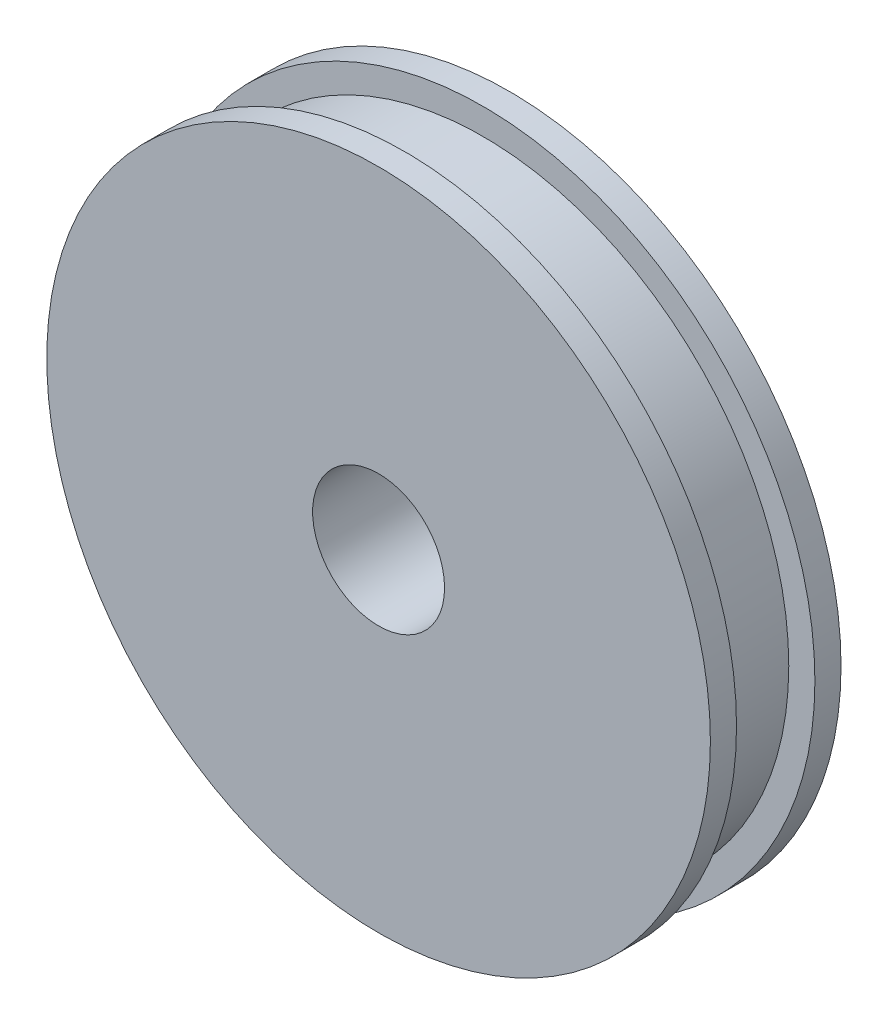
SolidWorks part; units mm, degrees
ref_plane "Alzado" through (0, 0, 0) normal (0, 0, 1) x (1, 0, 0)
ref_plane "Planta" through (0, 0, 0) normal (0, 1, 0) x (1, 0, 0)
ref_plane "Vista lateral" through (0, 0, 0) normal (1, 0, 0) x (0, 0, -1)
sketch "Croquis1" plane through (0, 0, 0) normal (0, 0, 1) x (1, 0, 0)
  circle A0 centre (0, 0) radius 25.4
  circle A1 centre (0, 0) radius 5.05
  dimension "D1" = 50.8
  dimension "D2" = 10.1
extrude "Saliente-Extruir1" add sketch "Croquis1" along normal blind 10
sketch "Croquis2" plane through (0, 0, 0) normal (1, 0, 0) x (0, 0, -1)
  line L0 (0, 25.4) -> (-10, 25.4) construction
  line L1 (-2, 25.4) -> (-8, 25.4)
  line L2 (-2, 25.4) -> (-2, 23.4)
  line L3 (-2, 23.4) -> (-8, 23.4)
  line L4 (-8, 25.4) -> (-8, 23.4)
  line L5 (0, -25.4) -> (0, 25.4) construction
  line L6 (-10, 25.4) -> (-10, -25.4) construction
  dimension "D1" = 2
  dimension "D2" = 2
  dimension "D3" = 2
ref_axis "Eje1" through (0, 0, 10) along (0, 0, -1)
revolve "Cortar-Revolución1" cut sketch "Croquis2" angle 360 about axis through (0, 0, 10) along (0, 0, -1)
